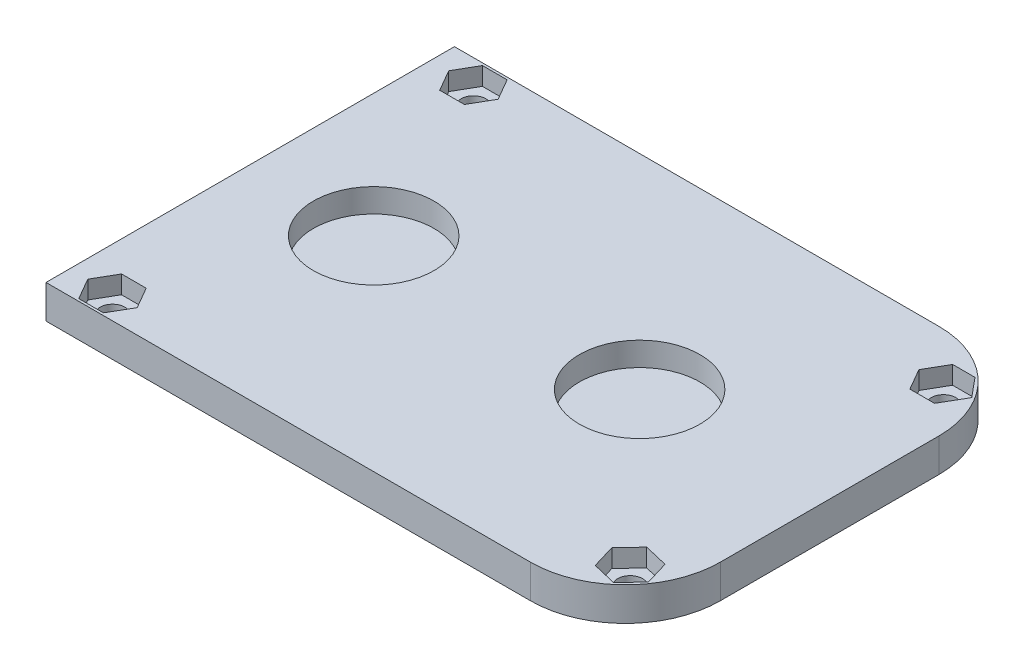
SolidWorks part; units mm, degrees
ref_plane "Front Plane" through (0, 0, 0) normal (0, 0, 1) x (1, 0, 0)
ref_plane "Top Plane" through (0, 0, 0) normal (0, 1, 0) x (1, 0, 0)
ref_plane "Right Plane" through (0, 0, 0) normal (1, 0, 0) x (0, 0, -1)
sketch "Sketch1" plane through (0, 0, 0) normal (0, 1, 0) x (1, 0, 0)
  line L0 (-8.3796, 28.6087) -> (58.9304, 28.6087)
  line L1 (71.6304, 15.9087) -> (71.6304, -13.3013)
  line L2 (58.9304, -26.0013) -> (-8.3796, -26.0013)
  line L3 (-14.7296, -19.6513) -> (-14.7296, 22.2587)
  arc A0 (71.6304, -13.3013) -> (58.9304, -26.0013) centre (58.9304, -13.3013) cw
  arc A1 (58.9304, 28.6087) -> (71.6304, 15.9087) centre (58.9304, 15.9087) cw
  arc A2 (-8.3796, -26.0013) -> (-14.7296, -19.6513) centre (-8.3796, -19.6513) cw
  arc A3 (-8.3796, 28.6087) -> (-14.7296, 22.2587) centre (-8.3796, 22.2587) ccw
  point P6 (71.6304, -26.0013)
  point P9 (71.6304, 28.6087)
  point P12 (-14.7296, -26.0013)
  dimension "D3" = 12.7
  dimension "D4" = 6.35
  dimension "D1" = 54.61
  dimension "D2" = 86.36
extrude "Boss-Extrude1" add sketch "Sketch1" along normal blind 4.476
sketch "Sketch2" plane through (0, 4.476, 0) normal (0, 1, 0) x (1, 0, 0)
  line L0 (65.9154, 22.2587) -> (65.9154, -19.6513)
  line L1 (64.2656, 19.4012) -> (67.5651, 19.4012)
  line L2 (-8.3796, -26.0013) -> (58.9304, -26.0013) construction
  line L3 (67.2573, 25.1162) -> (64.2656, 25.1162)
  line L5 (-14.7296, 22.2587) -> (-14.7296, -19.6513) construction
  line L6 (-14.7296, 22.2587) -> (-14.7296, -19.6513)
  line L7 (-0.1246, 25.4337) -> (-0.1246, -22.8263)
  line L8 (69.3847, 22.5527) -> (67.2573, 25.1162)
  line L9 (69.1257, -20.4133) -> (68.1804, -17.252)
  line L10 (68.1804, -17.252) -> (64.9701, -16.4901)
  line L11 (64.9701, -16.4901) -> (62.705, -18.8893)
  line L12 (62.705, -18.8893) -> (63.6503, -22.0506)
  line L13 (63.6503, -22.0506) -> (66.8606, -22.8126)
  line L14 (66.8606, -22.8126) -> (69.1257, -20.4133)
  line L15 (64.2656, 25.1162) -> (62.6158, 22.2587)
  line L16 (62.6158, 22.2587) -> (64.2656, 19.4012)
  line L17 (67.5651, 19.4012) -> (69.3847, 22.5527)
  line L18 (-1.7744, 22.5762) -> (1.5251, 22.5762)
  line L19 (1.5251, 28.2912) -> (-1.7744, 28.2912)
  line L20 (-1.7744, 28.2912) -> (-3.4242, 25.4337)
  line L21 (-3.4242, 25.4337) -> (-1.7744, 22.5762)
  line L22 (3.1749, 25.4337) -> (1.5251, 28.2912)
  line L23 (1.5251, 22.5762) -> (3.1749, 25.4337)
  line L24 (-1.7744, -25.6838) -> (1.5251, -25.6838)
  line L25 (1.5251, -19.9688) -> (-1.7744, -19.9688)
  line L26 (-1.7744, -19.9688) -> (-3.4242, -22.8263)
  line L27 (-3.4242, -22.8263) -> (-1.7744, -25.6838)
  line L28 (3.1749, -22.8263) -> (1.5251, -19.9688)
  line L29 (1.5251, -25.6838) -> (3.1749, -22.8263)
  circle A0 centre (65.9154, -19.6513) radius 2.8575 construction
  circle A1 centre (65.9154, 22.2587) radius 2.8575 construction
  circle A2 centre (-0.1246, 25.4337) radius 2.8575 construction
  circle A3 centre (-0.1246, -22.8263) radius 2.8575 construction
  dimension "D1" = 6.35
  dimension "D2" = 48.26
  dimension "D3" = 80.645
  dimension "D4" = 3.175
  dimension "D5" = 51.435
  dimension "D6" = 14.605
  dimension "D7" = 5.715
extrude "Cut-Extrude1" cut sketch "Sketch2" against normal blind 2.413 contours L22 L19 L20 L21 L18 L23 | L8 L3 L15 L16 L1 L17 | L9 L10 L11 L12 L13 L14 | L28 L25 L26 L27 L24 L29
sketch "Sketch4" plane through (0, 4.476, 0) normal (0, 1, 0) x (1, 0, 0)
  circle A0 centre (-0.1246, 25.4337) radius 1.65
  circle A1 centre (-0.1246, -22.8263) radius 1.65
  circle A2 centre (65.9154, -19.6513) radius 1.65
  circle A3 centre (65.9154, 22.2587) radius 1.65
  dimension "D1" = 3.3
  dimension "D2" = 3.3
  dimension "D3" = 3.3
  dimension "D4" = 3.3
extrude "Cut-Extrude2" cut sketch "Sketch4" against normal through all
sketch "Sketch5" plane through (0, 4.476, 0) normal (0, 1, 0) x (1, 0, 0)
  line L0 (-14.7296, 1.3037) -> (71.6304, 1.3037)
  line L1 (-14.7296, -19.6513) -> (-14.7296, 22.2587) construction
  line L2 (71.6304, 15.9087) -> (71.6304, -13.3013) construction
  circle A0 centre (46.2304, 1.3037) radius 8.0645
  circle A1 centre (10.6704, 1.3037) radius 8.0645
  dimension "D1" = 16.129
  dimension "D2" = 25.4
  dimension "D3" = 25.4
extrude "Cut-Extrude3" cut sketch "Sketch5" against normal blind 3.175 contours L0 A1 | L0 A1 | L0 A0 | L0 A0
sketch "Sketch6" plane through (0, 4.476, 0) normal (0, 1, 0) x (1, 0, 0)
  line L0 (-5.8396, 32.7975) -> (-5.8396, -29.7624)
  line L1 (-5.8396, -29.7624) -> (-22.8237, -29.7624)
  line L2 (-22.8237, -29.7624) -> (-22.8237, 32.7975)
  line L3 (-22.8237, 32.7975) -> (-5.8396, 32.7975)
  line L4 (-14.7296, -19.6513) -> (-14.7296, 22.2587) construction
  dimension "D1" = 8.89
extrude "Cut-Extrude4" cut sketch "Sketch6" against normal through all
